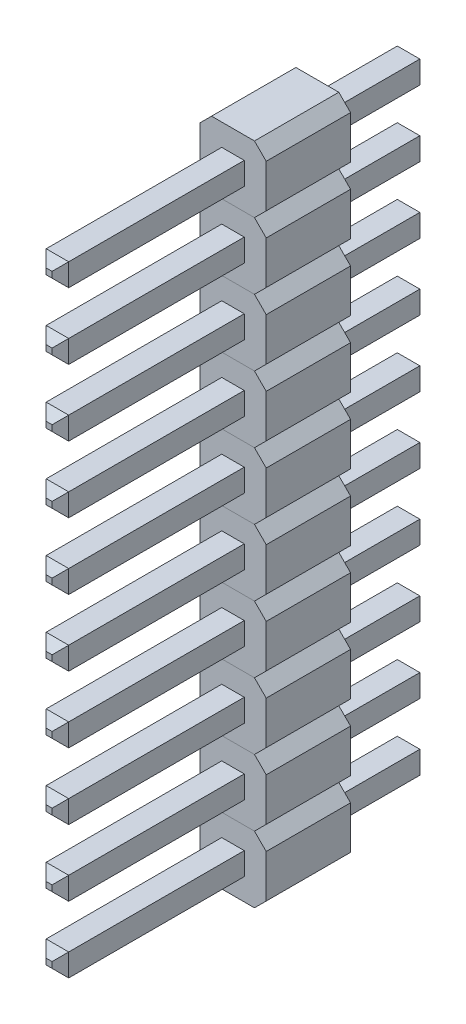
SolidWorks part; units mm, degrees
ref_plane "Alzado" through (0, 0, 0) normal (0, 0, 1) x (1, 0, 0)
ref_plane "Planta" through (0, 0, 0) normal (0, 1, 0) x (1, 0, 0)
ref_plane "Vista lateral" through (0, 0, 0) normal (1, 0, 0) x (0, 0, -1)
sketch "pin_drawing" plane through (0, 0, 0) normal (0, 0, 1) x (1, 0, 0)
  line L0 (0, -1) -> (0, 1) construction
  line L1 (-0.6464, 1) -> (0.6464, 1)
  line L2 (-1, 0.6464) -> (-1, -0.6464)
  line L3 (-1, 0.6464) -> (-0.6464, 1)
  line L4 (0, 0) -> (-1.1007, 0.0207) construction
  line L5 (-0.3394, -0.3394) -> (0.3394, 0.3394) construction
  line L6 (1, 0.6464) -> (1, -0.6464)
  line L7 (0, 0) -> (0.8993, 0.0207) construction
  line L8 (1, -0.6464) -> (0.6464, -1)
  line L9 (0.6464, 1) -> (1, 0.6464)
  line L11 (-0.6464, -1) -> (-1, -0.6464)
  line L12 (-0.3394, 0.3394) -> (0.3394, 0.3394)
  line L13 (-0.3394, 0.3394) -> (-0.3394, -0.3394)
  line L14 (-0.3394, -0.3394) -> (0.3394, -0.3394)
  line L15 (0.3394, 0.3394) -> (0.3394, -0.3394)
  line L16 (0, 0) -> (0.3394, -0.3394) construction
  line L17 (0, 0) -> (-0.3394, 0.3394) construction
  line L18 (0.6464, -1) -> (-0.6464, -1)
  dimension "D4" = 135
  dimension "D5" = 0.5
  dimension "D7" = 2
  dimension "D8" = 2
extrude "Boss-Extrude1" add sketch "pin_drawing" along normal blind 2.54
sketch "Sketch1" plane through (0, 0, 2.54) normal (0, 0, 1) x (1, 0, 0)
  line L0 (-0.3394, 0.3394) -> (-0.3394, -0.3394) construction
  line L1 (0.3394, -0.3394) -> (0.3394, 0.3394) construction
  line L2 (0.3394, 0.3394) -> (-0.3394, 0.3394) construction
  line L3 (-0.3394, -0.3394) -> (0.3394, -0.3394) construction
  line L4 (0.3394, -0.3394) -> (0.3394, 0.3394)
  line L5 (0.3394, 0.3394) -> (-0.3394, 0.3394)
  line L6 (-0.3394, -0.3394) -> (0.3394, -0.3394)
  line L7 (-0.3394, 0.3394) -> (-0.3394, -0.3394)
extrude "Boss-Extrude2" add sketch "Sketch1" along normal blind 5.5372 and the other way blind 5.5372 separate body
chamfer "Chamfer1" distance 0.25 angle 45 8 edges at (0.3394, 0, -2.9972) (0, 0.3394, -2.9972) (-0.3394, 0, -2.9972) (0, -0.3394, -2.9972) (-0.3394, 0, 8.0772) (0, 0.3394, 8.0772) (0.3394, 0, 8.0772) (0, -0.3394, 8.0772)
pattern_linear "LPattern2" count 10 spacing 2 along (0, -1, 0) of bodies 105 103
